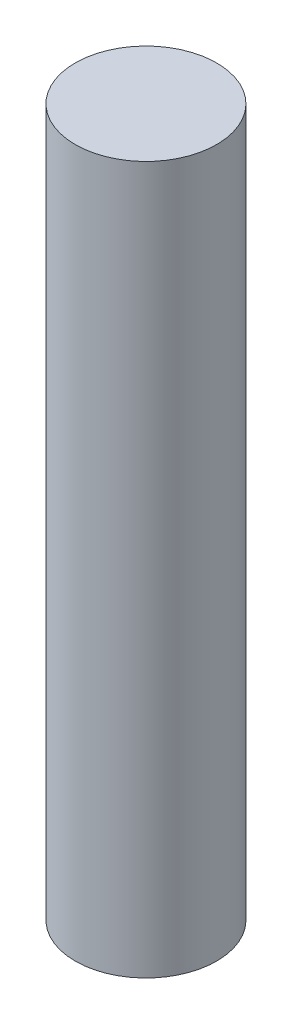
SolidWorks part; units mm, degrees
ref_plane "Front Plane" through (0, 0, 0) normal (0, 0, 1) x (1, 0, 0)
ref_plane "Top Plane" through (0, 0, 0) normal (0, 1, 0) x (1, 0, 0)
ref_plane "Right Plane" through (0, 0, 0) normal (1, 0, 0) x (0, 0, -1)
sketch "Sketch1" plane through (0, 0, 0) normal (0, 1, 0) x (1, 0, 0)
  circle A0 centre (0, 0) radius 45
  dimension "D1" = 90
extrude "Boss-Extrude1" add sketch "Sketch1" along normal blind 450 contours A0
